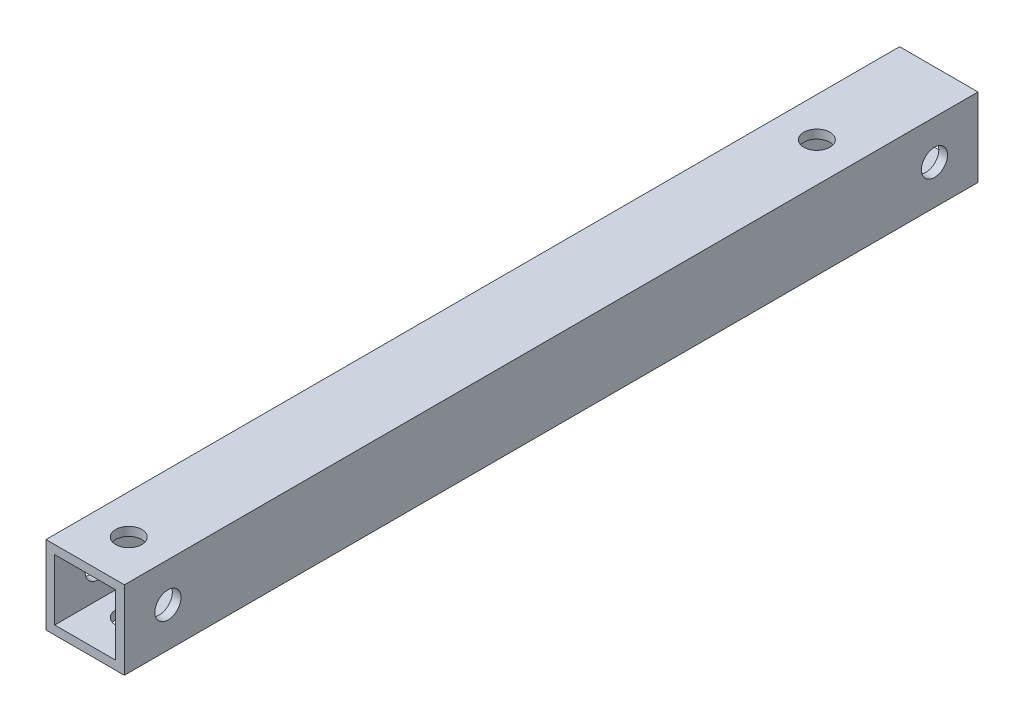
SolidWorks part; units mm, degrees
ref_plane "正面" through (0, 0, 0) normal (0, 0, 1) x (1, 0, 0)
ref_plane "平面" through (0, 0, 0) normal (0, 1, 0) x (1, 0, 0)
ref_plane "右側面" through (0, 0, 0) normal (1, 0, 0) x (0, 0, -1)
sketch "ｽｹｯﾁ1" plane through (0, 0, 0) normal (0, 0, 1) x (1, 0, 0)
  line L1 (-4.5, 4.5) -> (4.5, 4.5)
  line L2 (-4.5, 4.5) -> (-4.5, -4.5)
  line L3 (-4.5, -4.5) -> (4.5, -4.5)
  line L4 (4.5, 4.5) -> (4.5, -4.5)
  line L5 (-4.5, 4.5) -> (4.5, -4.5) construction
  line L6 (-4.5, -4.5) -> (4.5, 4.5) construction
  point P0 (0, 0)
  dimension "D1" = 9
  dimension "D2" = 9
extrude "ﾎﾞｽ - 押し出し1" add sketch "ｽｹｯﾁ1" along normal blind 98
sketch "ｽｹｯﾁ2" plane through (0, 0, 98) normal (0, 0, 1) x (1, 0, 0)
  line L1 (-3.5, 3.5) -> (3.5, 3.5)
  line L2 (-3.5, 3.5) -> (-3.5, -3.5)
  line L3 (-3.5, -3.5) -> (3.5, -3.5)
  line L4 (3.5, 3.5) -> (3.5, -3.5)
  line L5 (-3.5, 3.5) -> (3.5, -3.5) construction
  line L6 (-3.5, -3.5) -> (3.5, 3.5) construction
  point P0 (0, 0)
  dimension "D1" = 7
  dimension "D2" = 7
extrude "ｶｯﾄ - 押し出し1" cut sketch "ｽｹｯﾁ2" against normal blind 106.6
sketch "ｽｹｯﾁ3" plane through (0, 4.5, 0) normal (0, 1, 0) x (1, 0, 0)
  line L0 (0, -98) -> (0, -93)
  line L1 (4.5, -98) -> (-4.5, -98) construction
  line L2 (0, 0) -> (0, -14)
  circle A0 centre (0, -93) radius 1.5
  circle A1 centre (0, -14) radius 1.5
  dimension "D2" = 3
  dimension "D4" = 3
  dimension "D1" = 14
  dimension "D3" = 5
extrude "ｶｯﾄ - 押し出し2" cut sketch "ｽｹｯﾁ3" against normal blind 106.6
sketch "ｽｹｯﾁ4" plane through (-4.5, 0, 0) normal (-1, 0, 0) x (0, 0, 1)
  line L0 (0, 0) -> (5, 0)
  line L1 (98, 0) -> (93, 0)
  line L2 (98, 4.5) -> (98, -4.5) construction
  circle A0 centre (5, 0) radius 1.5
  circle A1 centre (93, 0) radius 1.5
  dimension "D3" = 3
  dimension "D4" = 3
  dimension "D1" = 5
  dimension "D2" = 5
extrude "ｶｯﾄ - 押し出し4" cut sketch "ｽｹｯﾁ4" against normal blind 50
